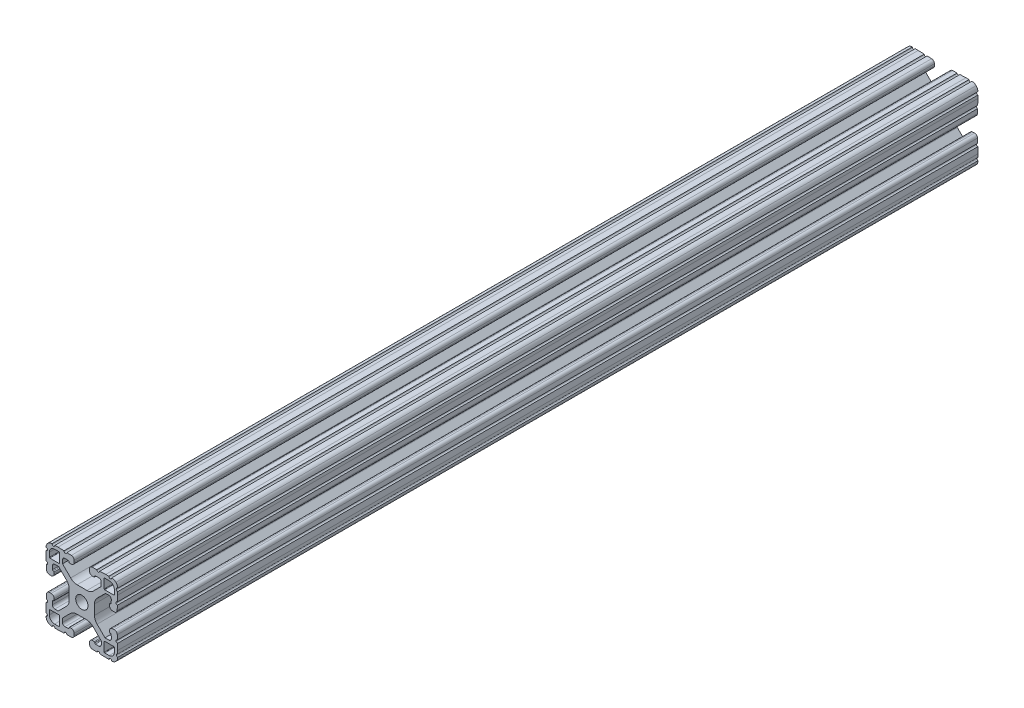
SolidWorks part; units mm, degrees
material "6061-T6 (SS)"
ref_plane "Front Plane" through (0, 0, 0) normal (0, 0, 1) x (1, 0, 0)
ref_plane "Top Plane" through (0, 0, 0) normal (0, 1, 0) x (1, 0, 0)
ref_plane "Right Plane" through (0, 0, 0) normal (1, 0, 0) x (0, 0, -1)
ref_plane "Plane1" through (0, 0, -25.4) normal (0, 0, -1) x (-1, 0, 0)
sketch "Sketch1" plane through (0, 0, -25.4) normal (0, 0, -1) x (-1, 0, 0)
  line L0 (-83.3577, 88.2941) -> (-83.3577, 93.1709)
  line L1 (-83.1037, 93.4249) -> (-80.767, 93.4249)
  line L2 (-77.9729, 90.6309) -> (-77.9729, 88.2941)
  line L3 (-78.2269, 88.0401) -> (-83.1037, 88.0401)
  line L4 (-83.3577, 59.2291) -> (-83.3577, 64.1059)
  line L5 (-83.1037, 64.3599) -> (-78.2269, 64.3599)
  line L6 (-77.9729, 64.1059) -> (-77.9729, 61.7691)
  line L7 (-80.767, 58.9751) -> (-83.1037, 58.9751)
  line L8 (-107.1423, 93.1709) -> (-107.1423, 88.2941)
  line L9 (-107.3963, 88.0401) -> (-112.2731, 88.0401)
  line L10 (-112.5271, 88.2941) -> (-112.5271, 90.6309)
  line L11 (-109.733, 93.4249) -> (-107.3963, 93.4249)
  line L12 (-107.1423, 64.1059) -> (-107.1423, 59.2291)
  line L13 (-107.3963, 58.9751) -> (-109.733, 58.9751)
  line L14 (-112.5271, 61.7691) -> (-112.5271, 64.1059)
  line L15 (-112.2731, 64.3599) -> (-107.3963, 64.3599)
  line L16 (-88.0437, 91.8626) -> (-86.2967, 91.9236)
  line L17 (-84.9824, 90.6544) -> (-84.9824, 88.8002)
  line L18 (-84.9824, 88.8002) -> (-89.3066, 84.476)
  line L19 (-92.7196, 83.0295) -> (-97.9616, 83.0295)
  line L20 (-101.3202, 84.4207) -> (-105.516, 88.6165)
  line L21 (-105.516, 88.6165) -> (-105.516, 90.7313)
  line L22 (-104.2017, 92.0006) -> (-102.4547, 91.9396)
  line L23 (-101.7262, 91.1059) -> (-100.9297, 91.0781)
  line L24 (-99.2999, 92.6519) -> (-99.2999, 93.5668)
  line L25 (-100.8197, 95.1407) -> (-103.2119, 95.2242)
  line L26 (-104.735, 95.2774) -> (-107.9359, 95.3892)
  line L27 (-107.9359, 95.3892) -> (-109.5615, 95.3892)
  line L28 (-114.2859, 90.6648) -> (-114.2859, 89.0392)
  line L29 (-114.2859, 89.0392) -> (-114.1741, 85.8383)
  line L30 (-114.1209, 84.3152) -> (-114.0374, 81.9231)
  line L31 (-112.4635, 80.4032) -> (-111.5486, 80.4032)
  line L32 (-109.9748, 82.033) -> (-110.0026, 82.8295)
  line L33 (-110.8377, 83.5577) -> (-110.8987, 85.3047)
  line L34 (-109.6294, 86.619) -> (-107.8072, 86.619)
  line L35 (-107.8072, 86.619) -> (-103.3649, 82.1768)
  line L36 (-101.9737, 78.8182) -> (-101.9737, 73.576)
  line L37 (-103.3649, 70.2174) -> (-107.5607, 66.0217)
  line L38 (-107.5607, 66.0217) -> (-109.6524, 66.0217)
  line L39 (-110.9217, 67.336) -> (-110.8607, 69.083)
  line L40 (-110.0322, 69.8124) -> (-110.0043, 70.6089)
  line L41 (-111.5782, 72.2387) -> (-112.4931, 72.2387)
  line L42 (-114.0669, 70.7189) -> (-114.1505, 68.3267)
  line L43 (-114.2036, 66.8036) -> (-114.3154, 63.6027)
  line L44 (-114.3154, 63.6027) -> (-114.3154, 61.9626)
  line L45 (-109.6111, 57.1437) -> (-107.9855, 57.1437)
  line L46 (-107.9855, 57.1437) -> (-104.7846, 57.2555)
  line L47 (-103.2615, 57.3086) -> (-100.8694, 57.3922)
  line L48 (-99.3495, 58.966) -> (-99.3495, 59.8809)
  line L49 (-100.9794, 61.4548) -> (-101.7758, 61.4269)
  line L50 (-102.5054, 60.599) -> (-104.2524, 60.538)
  line L51 (-105.5667, 61.8072) -> (-105.5667, 63.6295)
  line L52 (-105.5667, 63.6295) -> (-101.1311, 68.065)
  line L53 (-97.7725, 69.4562) -> (-92.5304, 69.4562)
  line L54 (-89.1717, 68.065) -> (-84.976, 63.8692)
  line L55 (-84.976, 63.8692) -> (-84.976, 61.7811)
  line L56 (-86.2903, 60.5118) -> (-88.0373, 60.5728)
  line L57 (-88.7596, 61.4332) -> (-89.5561, 61.461)
  line L58 (-91.1859, 59.8872) -> (-91.1859, 58.9723)
  line L59 (-89.6661, 57.3985) -> (-87.2739, 57.3149)
  line L60 (-85.7508, 57.2617) -> (-82.5499, 57.15)
  line L61 (-82.5499, 57.15) -> (-80.9244, 57.15)
  line L62 (-76.2, 61.8744) -> (-76.2, 63.4999)
  line L63 (-76.2, 63.4999) -> (-76.3117, 66.7008)
  line L64 (-76.3649, 68.2239) -> (-76.4484, 70.6161)
  line L65 (-78.0223, 72.1359) -> (-78.9372, 72.1359)
  line L66 (-80.511, 70.5061) -> (-80.4832, 69.7096)
  line L67 (-79.6552, 68.9801) -> (-79.5942, 67.2331)
  line L68 (-80.8634, 65.9188) -> (-82.6857, 65.9188)
  line L69 (-82.6857, 65.9188) -> (-87.1213, 70.3543)
  line L70 (-88.5125, 73.7128) -> (-88.5126, 78.955)
  line L71 (-87.1214, 82.3137) -> (-82.9257, 86.5095)
  line L72 (-82.9257, 86.5095) -> (-80.8375, 86.5095)
  line L73 (-79.5682, 85.1951) -> (-79.6293, 83.4482)
  line L74 (-80.4896, 82.7258) -> (-80.5175, 81.9294)
  line L75 (-78.9436, 80.2995) -> (-78.0287, 80.2995)
  line L76 (-76.4549, 81.8194) -> (-76.3713, 84.2115)
  line L77 (-76.3182, 85.7346) -> (-76.2064, 88.9355)
  line L78 (-76.2064, 88.9355) -> (-76.2064, 90.5611)
  line L79 (-80.9308, 95.2855) -> (-82.5564, 95.2855)
  line L80 (-82.5564, 95.2855) -> (-85.7573, 95.1737)
  line L81 (-87.2803, 95.1205) -> (-89.6725, 95.037)
  line L82 (-91.1924, 93.4632) -> (-91.1924, 92.5483)
  line L83 (-89.5625, 90.9744) -> (-88.7661, 91.0023)
  arc A0 (-83.3577, 93.1709) -> (-83.1037, 93.4249) centre (-83.1037, 93.1709) cw
  arc A1 (-80.767, 93.4249) -> (-77.9729, 90.6309) centre (-80.7669, 90.6309) cw
  arc A2 (-77.9729, 88.2941) -> (-78.2269, 88.0401) centre (-78.2269, 88.2941) cw
  arc A3 (-83.1037, 88.0401) -> (-83.3577, 88.2941) centre (-83.1037, 88.2941) cw
  arc A4 (-83.1037, 58.9751) -> (-83.3577, 59.2291) centre (-83.1037, 59.2291) cw
  arc A5 (-83.3577, 64.1059) -> (-83.1037, 64.3599) centre (-83.1037, 64.1059) cw
  arc A6 (-78.2269, 64.3599) -> (-77.9729, 64.1059) centre (-78.2269, 64.1059) cw
  arc A7 (-77.9729, 61.7691) -> (-80.767, 58.9751) centre (-80.7669, 61.7691) cw
  arc A8 (-107.3963, 93.4249) -> (-107.1423, 93.1709) centre (-107.3963, 93.1709) cw
  arc A9 (-107.1423, 88.2941) -> (-107.3963, 88.0401) centre (-107.3963, 88.2941) cw
  arc A10 (-112.2731, 88.0401) -> (-112.5271, 88.2941) centre (-112.2731, 88.2941) cw
  arc A11 (-112.5271, 90.6309) -> (-109.733, 93.4249) centre (-109.7331, 90.6309) cw
  arc A12 (-107.1423, 59.2291) -> (-107.3963, 58.9751) centre (-107.3963, 59.2291) cw
  arc A13 (-109.733, 58.9751) -> (-112.5271, 61.7691) centre (-109.7331, 61.7691) cw
  arc A14 (-112.5271, 64.1059) -> (-112.2731, 64.3599) centre (-112.2731, 64.1059) cw
  arc A15 (-107.3963, 64.3599) -> (-107.1423, 64.1059) centre (-107.3963, 64.1059) cw
  circle A16 centre (-95.25, 76.2) radius 3.2639
  arc A17 (-88.7661, 91.0023) -> (-88.3984, 91.383) centre (-88.7794, 91.383) ccw
  arc A18 (-88.3984, 91.383) -> (-88.0437, 91.8626) centre (-88.0304, 91.4819) cw
  arc A19 (-86.2967, 91.9236) -> (-84.9824, 90.6544) centre (-86.2524, 90.6544) cw
  arc A20 (-89.3066, 84.476) -> (-92.7196, 83.0295) centre (-92.7196, 87.7793) cw
  arc A21 (-97.9616, 83.0295) -> (-101.3202, 84.4207) centre (-97.9616, 87.7793) cw
  arc A22 (-105.516, 90.7313) -> (-104.2017, 92.0006) centre (-104.246, 90.7313) cw
  arc A23 (-102.4547, 91.9396) -> (-102.087, 91.5588) centre (-102.468, 91.5588) cw
  arc A24 (-102.087, 91.5588) -> (-101.7262, 91.1059) centre (-101.7129, 91.4867) ccw
  arc A25 (-100.9297, 91.0781) -> (-99.2999, 92.6519) centre (-100.8747, 92.6519) ccw
  arc A26 (-99.2999, 93.5668) -> (-100.8197, 95.1407) centre (-100.8747, 93.5668) ccw
  arc A27 (-103.2119, 95.2242) -> (-104.735, 95.2774) centre (-103.9735, 95.2508) cw
  arc A28 (-109.5615, 95.3892) -> (-111.0855, 95.3892) centre (-110.3235, 95.3892) cw
  arc A29 (-111.0855, 95.3892) -> (-113.3432, 94.4465) centre (-111.0855, 92.2142) ccw
  arc A30 (-113.3432, 94.4465) -> (-114.2859, 92.1888) centre (-111.1109, 92.1888) ccw
  arc A31 (-114.2859, 92.1888) -> (-114.2859, 90.6648) centre (-114.2859, 91.4268) cw
  arc A32 (-114.1741, 85.8383) -> (-114.1209, 84.3152) centre (-114.1475, 85.0768) cw
  arc A33 (-114.0374, 81.9231) -> (-112.4635, 80.4032) centre (-112.4635, 81.978) ccw
  arc A34 (-111.5486, 80.4032) -> (-109.9748, 82.033) centre (-111.5486, 81.978) ccw
  arc A35 (-110.0026, 82.8295) -> (-110.3834, 83.1972) centre (-110.3834, 82.8162) ccw
  arc A36 (-110.3834, 83.1972) -> (-110.8377, 83.5577) centre (-110.4569, 83.571) cw
  arc A37 (-110.8987, 85.3047) -> (-109.6294, 86.619) centre (-109.6294, 85.349) cw
  arc A38 (-103.3649, 82.1768) -> (-101.9737, 78.8182) centre (-106.7235, 78.8182) cw
  arc A39 (-101.9737, 73.576) -> (-103.3649, 70.2174) centre (-106.7235, 73.576) cw
  arc A40 (-109.6524, 66.0217) -> (-110.9217, 67.336) centre (-109.6524, 67.2917) cw
  arc A41 (-110.8607, 69.083) -> (-110.4799, 69.4507) centre (-110.4799, 69.0697) cw
  arc A42 (-110.4799, 69.4507) -> (-110.0322, 69.8124) centre (-110.413, 69.8257) ccw
  arc A43 (-110.0043, 70.6089) -> (-111.5782, 72.2387) centre (-111.5782, 70.6639) ccw
  arc A44 (-112.4931, 72.2387) -> (-114.0669, 70.7189) centre (-112.4931, 70.6639) ccw
  arc A45 (-114.1505, 68.3267) -> (-114.2036, 66.8036) centre (-114.1771, 67.5652) cw
  arc A46 (-114.3154, 61.9626) -> (-114.3332, 60.4644) centre (-114.4639, 61.2152) cw
  arc A47 (-114.3332, 60.4644) -> (-113.3928, 58.0864) centre (-111.1605, 60.3441) ccw
  arc A48 (-113.3928, 58.0864) -> (-111.1351, 57.1437) centre (-111.1351, 60.3187) ccw
  arc A49 (-111.1351, 57.1437) -> (-109.6111, 57.1437) centre (-110.3731, 57.1437) cw
  arc A50 (-104.7846, 57.2555) -> (-103.2615, 57.3086) centre (-104.0231, 57.2821) cw
  arc A51 (-100.8694, 57.3922) -> (-99.3495, 58.966) centre (-100.9243, 58.966) ccw
  arc A52 (-99.3495, 59.8809) -> (-100.9794, 61.4548) centre (-100.9243, 59.8809) ccw
  arc A53 (-101.7758, 61.4269) -> (-102.1435, 61.0462) centre (-101.7625, 61.0462) ccw
  arc A54 (-102.1435, 61.0462) -> (-102.5054, 60.599) centre (-102.5187, 60.9797) cw
  arc A55 (-104.2524, 60.538) -> (-105.5667, 61.8072) centre (-104.2967, 61.8072) cw
  arc A56 (-101.1311, 68.065) -> (-97.7725, 69.4562) centre (-97.7725, 64.7064) cw
  arc A57 (-92.5304, 69.4562) -> (-89.1717, 68.065) centre (-92.5304, 64.7064) cw
  arc A58 (-84.976, 61.7811) -> (-86.2903, 60.5118) centre (-86.246, 61.7811) cw
  arc A59 (-88.0373, 60.5728) -> (-88.405, 60.9536) centre (-88.024, 60.9536) cw
  arc A60 (-88.405, 60.9536) -> (-88.7596, 61.4332) centre (-88.7729, 61.0524) ccw
  arc A61 (-89.5561, 61.461) -> (-91.1859, 59.8872) centre (-89.6111, 59.8872) ccw
  arc A62 (-91.1859, 58.9723) -> (-89.6661, 57.3985) centre (-89.6111, 58.9723) ccw
  arc A63 (-87.2739, 57.3149) -> (-85.7508, 57.2617) centre (-86.5124, 57.2883) cw
  arc A64 (-80.9244, 57.15) -> (-79.4004, 57.15) centre (-80.1624, 57.15) cw
  arc A65 (-79.4004, 57.15) -> (-77.1426, 58.0927) centre (-79.4004, 60.325) ccw
  arc A66 (-77.1426, 58.0927) -> (-76.2, 60.3504) centre (-79.375, 60.3504) ccw
  arc A67 (-76.2, 60.3504) -> (-76.2, 61.8744) centre (-76.2, 61.1124) cw
  arc A68 (-76.3117, 66.7008) -> (-76.3649, 68.2239) centre (-76.3383, 67.4624) cw
  arc A69 (-76.4484, 70.6161) -> (-78.0223, 72.1359) centre (-78.0223, 70.5611) ccw
  arc A70 (-78.9372, 72.1359) -> (-80.511, 70.5061) centre (-78.9372, 70.5611) ccw
  arc A71 (-80.4832, 69.7096) -> (-80.1024, 69.342) centre (-80.1024, 69.723) ccw
  arc A72 (-80.1024, 69.342) -> (-79.6552, 68.9801) centre (-80.036, 68.9668) cw
  arc A73 (-79.5942, 67.2331) -> (-80.8634, 65.9188) centre (-80.8634, 67.1888) cw
  arc A74 (-87.1213, 70.3543) -> (-88.5125, 73.7128) centre (-83.7627, 73.7129) cw
  arc A75 (-88.5126, 78.955) -> (-87.1214, 82.3137) centre (-83.7628, 78.9551) cw
  arc A76 (-80.8375, 86.5095) -> (-79.5682, 85.1951) centre (-80.8375, 85.2395) cw
  arc A77 (-79.6293, 83.4482) -> (-80.01, 83.0805) centre (-80.01, 83.4615) cw
  arc A78 (-80.01, 83.0805) -> (-80.4896, 82.7258) centre (-80.1089, 82.7125) ccw
  arc A79 (-80.5175, 81.9294) -> (-78.9436, 80.2995) centre (-78.9436, 81.8743) ccw
  arc A80 (-78.0287, 80.2995) -> (-76.4549, 81.8194) centre (-78.0287, 81.8743) ccw
  arc A81 (-76.3713, 84.2115) -> (-76.3182, 85.7346) centre (-76.3448, 84.9731) cw
  arc A82 (-76.2064, 90.5611) -> (-76.2064, 92.0851) centre (-76.2064, 91.3231) cw
  arc A83 (-76.2064, 92.0851) -> (-77.1491, 94.3428) centre (-79.3814, 92.0851) ccw
  arc A84 (-77.1491, 94.3428) -> (-79.4068, 95.2855) centre (-79.4068, 92.1105) ccw
  arc A85 (-79.4068, 95.2855) -> (-80.9308, 95.2855) centre (-80.1688, 95.2855) cw
  arc A86 (-85.7573, 95.1737) -> (-87.2803, 95.1205) centre (-86.5188, 95.1471) cw
  arc A87 (-89.6725, 95.037) -> (-91.1924, 93.4632) centre (-89.6176, 93.4632) ccw
  arc A88 (-91.1924, 92.5483) -> (-89.5625, 90.9744) centre (-89.6176, 92.5483) ccw
extrude "Boss-Extrude1" add sketch "Sketch1" against normal blind 457.2
